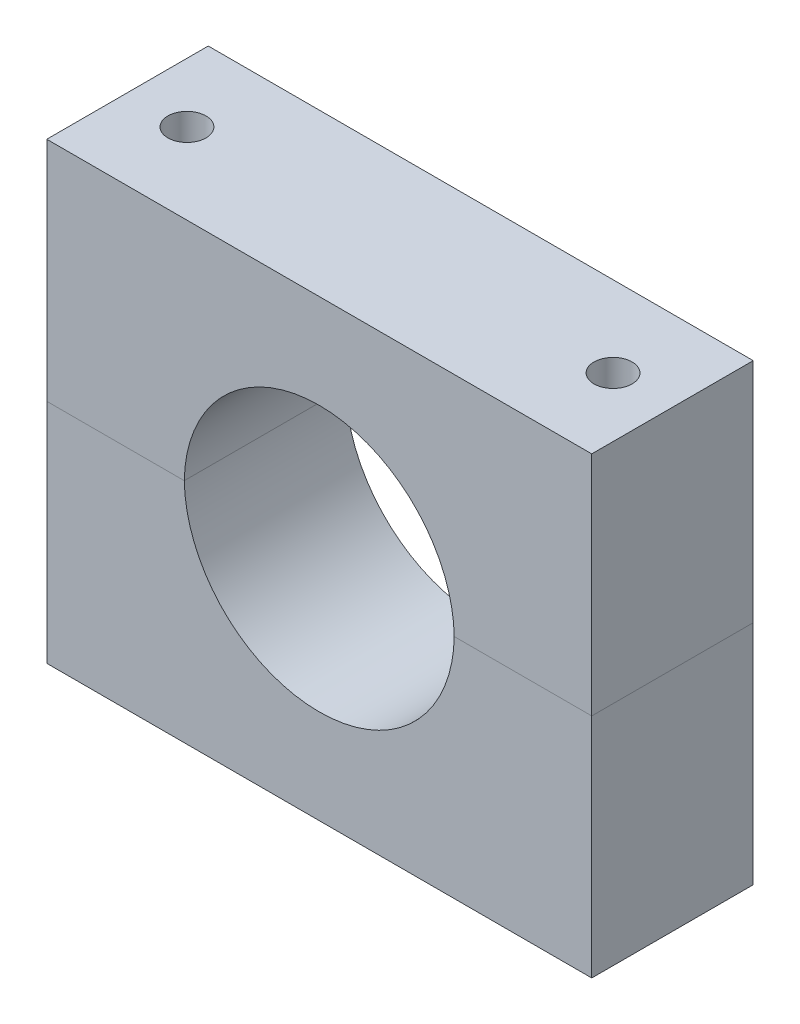
SolidWorks part; units mm, degrees
ref_plane "Plano frontal" through (0, 0, 0) normal (0, 0, 1) x (1, 0, 0)
ref_plane "Plano superior" through (0, 0, 0) normal (0, 1, 0) x (1, 0, 0)
ref_plane "Plano direito" through (0, 0, 0) normal (1, 0, 0) x (0, 0, -1)
sketch "Sketch1" plane through (0, 0, 0) normal (0, 0, 1) x (1, 0, 0)
  line L0 (5.6953, 36.0874) -> (-55.0547, 36.0874) construction
  line L1 (-55.0547, 57.0874) -> (66.4453, 57.0874)
  line L2 (-55.0547, 57.0874) -> (-55.0547, 5.9874)
  line L3 (-55.0547, 5.9874) -> (66.4453, 5.9874)
  line L4 (66.4453, 57.0874) -> (66.4453, 5.9874)
  circle A0 centre (5.6953, 5.9874) radius 30.1
  dimension "D3" = 60.2
  dimension "D1" = 121.5
  dimension "D2" = 21
extrude "Boss-Extrude1" add sketch "Sketch1" along normal blind 36 contours L0 A0 L3 L4 L1 L2 | A0 L0 L2 L3
sketch "Sketch3" plane through (-55.0547, 0, 0) normal (-1, 0, 0) x (0, 0, 1)
  line L0 (36, 57.0874) -> (36, 5.9874) construction
  line L1 (0, 5.9874) -> (36, 5.9874)
  line L2 (0, 5.9874) -> (0, 6.4874)
  line L3 (0, 6.4874) -> (36, 6.4874)
  line L4 (36, 5.9874) -> (36, 6.4874)
  dimension "D1" = 0.5
extrude "Cut-Extrude1" cut sketch "Sketch3" against normal through all
sketch "Sketch4" plane through (0, 57.0874, 0) normal (0, 1, 0) x (1, 0, 0)
  line L0 (66.4453, -18) -> (53.1953, -18) construction
  line L1 (-55.0547, -36) -> (-55.0547, 0) construction
  line L3 (-41.8047, -18) -> (-55.0547, -18) construction
  line L4 (66.4453, -36) -> (66.4453, 0) construction
  circle A0 centre (-41.8047, -18) radius 4.25
  circle A1 centre (53.1953, -18) radius 4.25
  dimension "D1" = 8.5
  dimension "D2" = 95
extrude "Cut-Extrude2" cut sketch "Sketch4" against normal through all
mirror "Mirror2" about plane through (66.4453, 6.4874, 0) normal (0, 1, 0) of bodies 103
